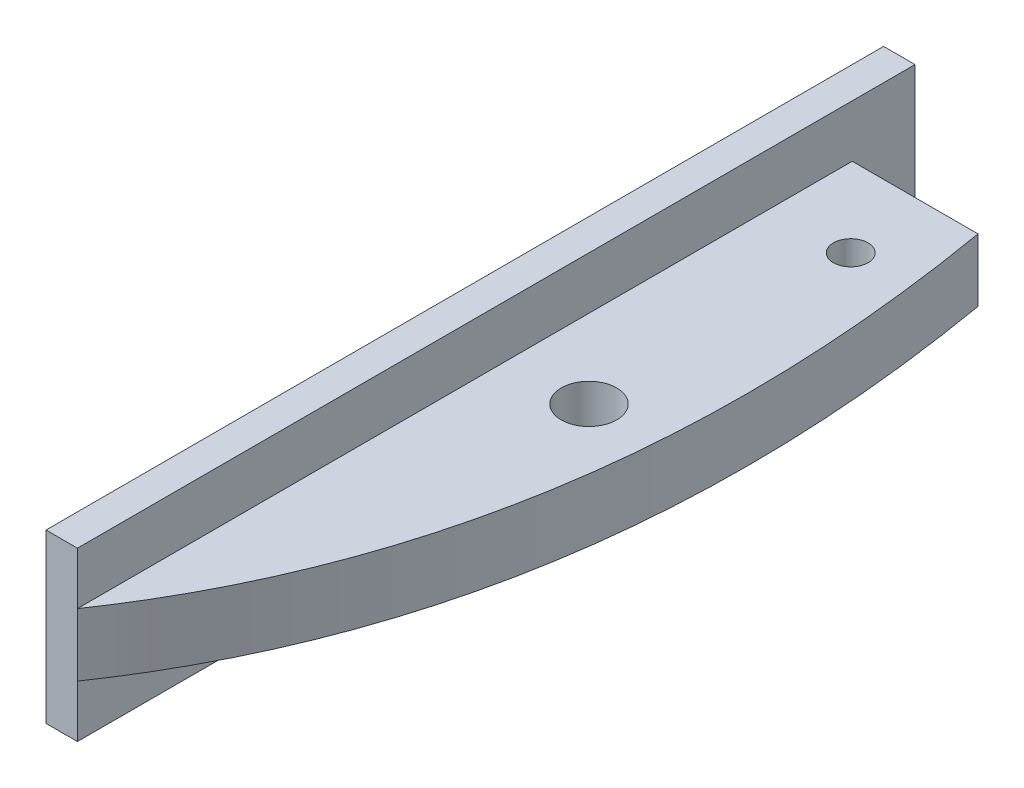
SolidWorks part; units mm, degrees
ref_plane "Front Plane" through (0, 0, 0) normal (0, 0, 1) x (1, 0, 0)
ref_plane "Top Plane" through (0, 0, 0) normal (0, 1, 0) x (1, 0, 0)
ref_plane "Right Plane" through (0, 0, 0) normal (1, 0, 0) x (0, 0, -1)
sketch "Sketch1" plane through (0, 0, 0) normal (0, 1, 0) x (1, 0, 0)
  line L0 (0, 0) -> (0, -84)
  line L1 (0, 0) -> (10, 0)
  circle A0 centre (7.5, -17.64) radius 1.65
  circle A1 centre (7.5, -42.64) radius 2.65
  spline S0 degree 2 poles (10, 0) (30.6713, -90.0857) (-50.3343, -120.2066) knots 0 0 0 1 1 1
  dimension "D5" = 3.3
  dimension "D7" = 5.3
  dimension "D1" = 84
  dimension "D2" = 10
  dimension "D3" = 17.64
  dimension "D4" = 7.5
  dimension "D6" = 42.64
  dimension "D8" = 7.5
extrude "Boss-Extrude1" add sketch "Sketch1" along normal blind 6 contours S0 L1 L0 A1 A0
sketch "Sketch2" plane through (0, 6, 0) normal (0, 1, 0) x (1, 0, 0)
  line L0 (0, 0) -> (0, -84) construction
  line L1 (-3, 0) -> (0, 0)
  line L2 (-3, 0) -> (-3, -84)
  line L3 (-3, -84) -> (0, -84)
  line L4 (0, 0) -> (0, -84)
  line L5 (-3, 0) -> (0, -84) construction
  line L6 (-3, -84) -> (0, 0) construction
  line L7 (0, 0) -> (10, 0) construction
  point P0 (-1.5, -42)
  dimension "D1" = 3
extrude "Boss-Extrude2" add sketch "Sketch2" along normal blind 5 and the other way blind 11
sketch "Sketch3" plane through (0, 6, 0) normal (0, 1, 0) x (1, 0, 0)
  line L0 (0, 0) -> (10, 0) construction
  line L1 (0, 0) -> (23.9812, 0)
  line L2 (0, 0) -> (0, -10)
  line L3 (0, -10) -> (23.9812, -10)
  line L4 (23.9812, 0) -> (23.9812, -10)
  line L5 (0, 0) -> (23.9812, -10) construction
  line L6 (0, -10) -> (23.9812, 0) construction
  line L7 (0, -84) -> (0, 0) construction
  line L8 (0, 0) -> (-3, 0) construction
  line L9 (-3.8727, 0) -> (0, 0)
  line L10 (-3.8727, 0) -> (-3.8727, -4)
  line L11 (-3.8727, -4) -> (0, -4)
  line L12 (0, 0) -> (0, -4)
  line L13 (-3.8727, 0) -> (0, -4) construction
  line L14 (-3.8727, -4) -> (0, 0) construction
  point P0 (11.9906, -5)
  point P10 (-1.9364, -2)
  spline M5 degree 2 poles (-50.3343, -120.2066) (30.6713, -90.0857) (10, 0) knots 0 0 0 1 1 1 only from (0, -84) to (10, 0)
  line M6 (10, 0) -> (0, 0)
  line M7 (0, 0) -> (0, -84)
  dimension "D1" = 0
  dimension "D2" = 10
  dimension "D3" = 4
extrude "Cut-Extrude2" cut sketch "Sketch3" against normal blind 20 and the other way blind 10 contours L4 L1 L3 M5 | L2 L3 M7 M5 M6 | L10 L11 L9 M7
